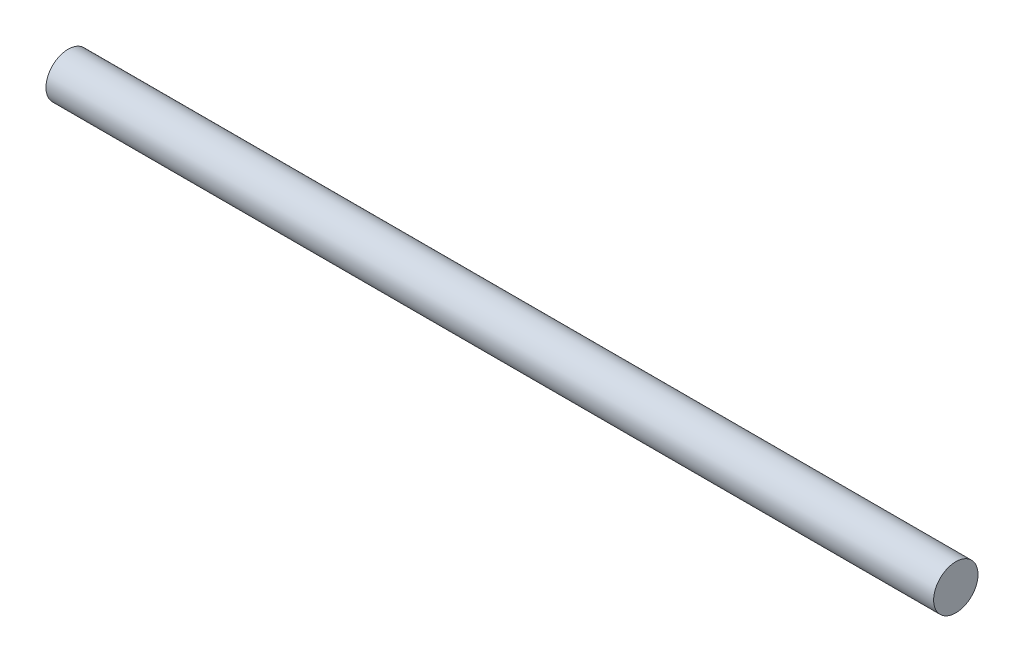
SolidWorks part; units mm, degrees
ref_plane "Front Plane" through (0, 0, 0) normal (0, 0, 1) x (1, 0, 0)
ref_plane "Top Plane" through (0, 0, 0) normal (0, 1, 0) x (1, 0, 0)
ref_plane "Right Plane" through (0, 0, 0) normal (1, 0, 0) x (0, 0, -1)
sketch "Sketch1" plane through (0, 0, 0) normal (1, 0, 0) x (0, 0, -1)
  circle A0 centre (0, 0) radius 1
  dimension "D1" = 2
extrude "DC MOTOR SHAFT" add sketch "Sketch1" along normal mid plane 40
